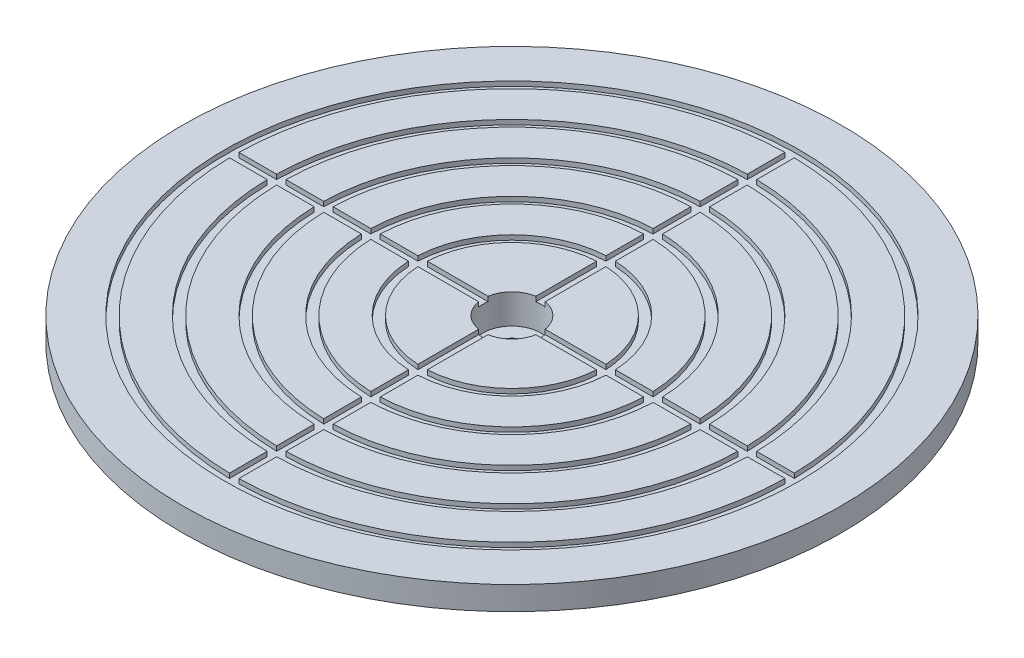
SolidWorks part; units mm, degrees
ref_plane "Front Plane" through (0, 0, 0) normal (0, 0, 1) x (1, 0, 0)
ref_plane "Top Plane" through (0, 0, 0) normal (0, 1, 0) x (1, 0, 0)
ref_plane "Right Plane" through (0, 0, 0) normal (1, 0, 0) x (0, 0, -1)
other "Center of Mass"
sketch "Sketch1" plane through (0, 0, 0) normal (0, 1, 0) x (1, 0, 0)
  circle A0 centre (0, 0) radius 15
  circle A1 centre (0, 0) radius 5.8
  dimension "D1" = 11.6
  dimension "D2" = 30
extrude "Boss-Extrude1" add sketch "Sketch1" along normal blind 22
sketch "Sketch2" plane through (0, 22, 0) normal (0, 1, 0) x (1, 0, 0)
  circle A1 centre (0, 0) radius 3.15
  circle A2 centre (0, 0) radius 70
  circle M1 centre (0, 0) radius 15
  circle M2 centre (0, 0) radius 5.8
  dimension "D1" = 6.3
  dimension "D2" = 140
extrude "Boss-Extrude2" add sketch "Sketch2" along normal blind 5 contours A2 M1 | A1 M2 | M1 M2
sketch "Sketch3" plane through (0, 27, 0) normal (0, 1, 0) x (1, 0, 0)
  circle A4 centre (0, 0) radius 10
  dimension "D1" = 20
sketch "Sketch4" plane through (0, 0, 0) normal (0, 0, 1) x (1, 0, 0)
  line L1 (9, 27) -> (11, 27)
  line L7 (10, 27) -> (-10, 27) construction
  line L8 (70, 27) -> (-70, 27) construction
  line L9 (11, 27) -> (10, 26)
  line L10 (10, 26) -> (9, 27)
  line L11 (10, 27) -> (10, 26) construction
  point P8 (10, 27)
  dimension "D1" = 10
  dimension "D2" = 2
  dimension "D3" = 1
sweep "Cut-Sweep1" [suppressed] cut profiles "Sketch4" path "Sketch3"
sketch "Sketch5" plane through (0, 27, 0) normal (0, 1, 0) x (1, 0, 0)
  circle A0 centre (0, 0) radius 20
  dimension "D1" = 40
sketch "Sketch6" plane through (0, 0, 0) normal (0, 0, 1) x (1, 0, 0)
  line L1 (19, 27) -> (21, 27)
  line L3 (19, 27) -> (19, 26)
  line L6 (20, 26) -> (20, 27) construction
  line L7 (20, 27) -> (-20, 27) construction
  line L8 (19, 26) -> (21, 26)
  line L9 (21, 26) -> (21, 27)
  dimension "D1" = 1
  dimension "D2" = 2
  dimension "D3" = 20
sweep "Cut-Sweep2" cut profiles "Sketch6" path "Sketch5"
sketch "Sketch7" plane through (0, 27, 0) normal (0, 1, 0) x (1, 0, 0)
  circle A0 centre (0, 0) radius 30
  dimension "D1" = 60
sketch "Sketch9" plane through (0, 0, 0) normal (0, 0, 1) x (1, 0, 0)
  line L0 (29, 27) -> (31, 27)
  line L1 (30, 27) -> (-30, 27) construction
  line L4 (29, 27) -> (29, 26)
  line L5 (29, 26) -> (31, 26)
  line L6 (31, 26) -> (31, 27)
  point P6 (30, 26)
  dimension "D1" = 30
  dimension "D2" = 2
  dimension "D3" = 1
sweep "Cut-Sweep5" cut profiles "Sketch9" path "Sketch7"
sketch "Sketch10" plane through (0, 27, 0) normal (0, 1, 0) x (1, 0, 0)
  circle A2 centre (0, 0) radius 40
  dimension "D1" = 80
sketch "Sketch11" plane through (0, 0, 0) normal (0, 0, 1) x (1, 0, 0)
  line L0 (39, 27) -> (41, 27)
  line L1 (70, 27) -> (-70, 27) construction
  line L4 (39, 27) -> (39, 26)
  line L5 (39, 26) -> (41, 26)
  line L6 (41, 26) -> (41, 27)
  point P4 (40, 26)
  dimension "D2" = 2
  dimension "D1" = 40
  dimension "D3" = 1
sweep "Cut-Sweep6" cut profiles "Sketch11" path "Sketch10"
sketch "Sketch12" plane through (0, 27, 0) normal (0, 1, 0) x (1, 0, 0)
  circle A0 centre (0, 0) radius 50
  dimension "D1" = 100
sketch "Sketch13" plane through (0, 0, 0) normal (0, 0, 1) x (1, 0, 0)
  line L0 (49, 27) -> (51, 27)
  line L3 (50, 27) -> (-50, 27) construction
  line L4 (50, 27) -> (50, 26) construction
  line L5 (49, 27) -> (49, 26)
  line L6 (49, 26) -> (51, 26)
  line L7 (51, 26) -> (51, 27)
  dimension "D2" = 2
  dimension "D1" = 1
  dimension "D3" = 50
sweep "Cut-Sweep7" cut profiles "Sketch13" path "Sketch12"
sketch "Sketch14" plane through (0, 0, 0) normal (0, 0, 1) x (1, 0, 0)
  line L0 (59, 27) -> (61, 27)
  line L2 (70, 27) -> (-70, 27) construction
  line L4 (60, 27) -> (60, 26) construction
  line L5 (59, 27) -> (59, 26)
  line L8 (61, 26) -> (61, 27)
  line L9 (59, 26) -> (61, 26)
  dimension "D2" = 2
  dimension "D1" = 1
  dimension "D3" = 60
sketch "Sketch15" plane through (0, 27, 0) normal (0, 1, 0) x (1, 0, 0)
  circle A0 centre (0, 0) radius 60
  dimension "D1" = 120
sweep "Cut-Sweep8" cut profiles "Sketch14" path "Sketch15"
sketch "Sketch18" plane through (0, 27, 0) normal (0, 1, 0) x (1, 0, 0)
  line L0 (0, 0) -> (-60, 0)
  line L1 (0, 0) -> (-51.9615, 30)
  line L2 (0, 0) -> (-30, 51.9615)
  line L3 (0, 0) -> (0, 60)
  line L4 (0, 0) -> (30, 51.9615)
  line L5 (0, 0) -> (51.9615, 30)
  line L6 (0, 0) -> (60, 0)
  line L7 (0, 0) -> (51.9615, -30)
  line L8 (0, 0) -> (30, -51.9615)
  line L9 (0, 0) -> (0, -60)
  line L10 (0, 0) -> (-30, -51.9615)
  line L11 (0, 0) -> (-51.9615, -30)
  line L12 (0, 0) -> (-60, 0) construction
  circle A2 centre (0, 0) radius 60 construction
  dimension "D1" = 120
  dimension "D2" = 12
sketch "Sketch20" plane through (0, 0, 0) normal (0, 0, 1) x (1, 0, 0)
  line L0 (-1, 27) -> (1, 27)
  line L1 (60, 27) -> (-60, 27) construction
  line L4 (0, 26) -> (0, 27) construction
  line L5 (-1, 27) -> (-1, 26)
  line L6 (-1, 26) -> (1, 26)
  line L7 (1, 26) -> (1, 27)
  point P7 (0, 27)
  dimension "D1" = 2
  dimension "D2" = 1
sweep "Cut-Sweep10" cut profiles "Sketch20" path "Sketch18"
pattern_circular "CirPattern1" count 4 over 360 about axis through (0, 0, 0) along (0, 1, 0) of "Cut-Sweep10"
sketch "Sketch27" plane through (0, 27, 0) normal (0, 1, 0) x (1, 0, 0)
  circle A0 centre (0, 0) radius 6.15
  dimension "D1" = 12.3
extrude "Cut-Extrude2" cut sketch "Sketch27" against normal blind 6.3
sketch "Sketch22" [suppressed] plane through (0, 27, 0) normal (0, 1, 0) x (1, 0, 0)
  circle A1 centre (0, 0) radius 90
  dimension "D1" = 180
extrude "Boss-Extrude3" [suppressed] add sketch "Sketch22" against normal blind 0.3
sketch "Sketch26" [suppressed] plane through (0, 26.7, 0) normal (0, -1, 0) x (1, 0, 0)
  circle A0 centre (0, 0) radius 68.5
  circle A1 centre (0, 0) radius 73.5
  circle A2 centre (0, 0) radius 67.5 construction
  dimension "D1" = 1
  dimension "D2" = 5
extrude "Boss-Extrude6" [suppressed] add sketch "Sketch26" along normal blind 2
sketch "Sketch28" plane through (0, 20.7, 0) normal (0, 1, 0) x (1, 0, 0)
  circle A0 centre (0, 0) radius 6.15
  circle A1 centre (0, 0) radius 3
  circle A2 centre (0, 0) radius 6.15 construction
  dimension "D1" = 6
extrude "Boss-Extrude7" add sketch "Sketch28" against normal blind 6
sketch "Sketch29" plane through (0, 22, 0) normal (0, -1, 0) x (1, 0, 0)
  circle A2 centre (0, 0) radius 60
  circle A4 centre (0, 0) radius 15 construction
  circle A5 centre (0, 0) radius 15
  circle M1 centre (0, 0) radius 15
  dimension "D1" = 120
extrude "Boss-Extrude8" add sketch "Sketch29" along normal blind 3 contours A2 M1
sketch "Sketch30" plane through (0, 19, 0) normal (0, -1, 0) x (1, 0, 0)
  circle A0 centre (0, 0) radius 45
  circle A1 centre (0, 0) radius 15
  circle A2 centre (0, 0) radius 15 construction
  dimension "D1" = 90
extrude "Boss-Extrude9" add sketch "Sketch30" along normal blind 3
